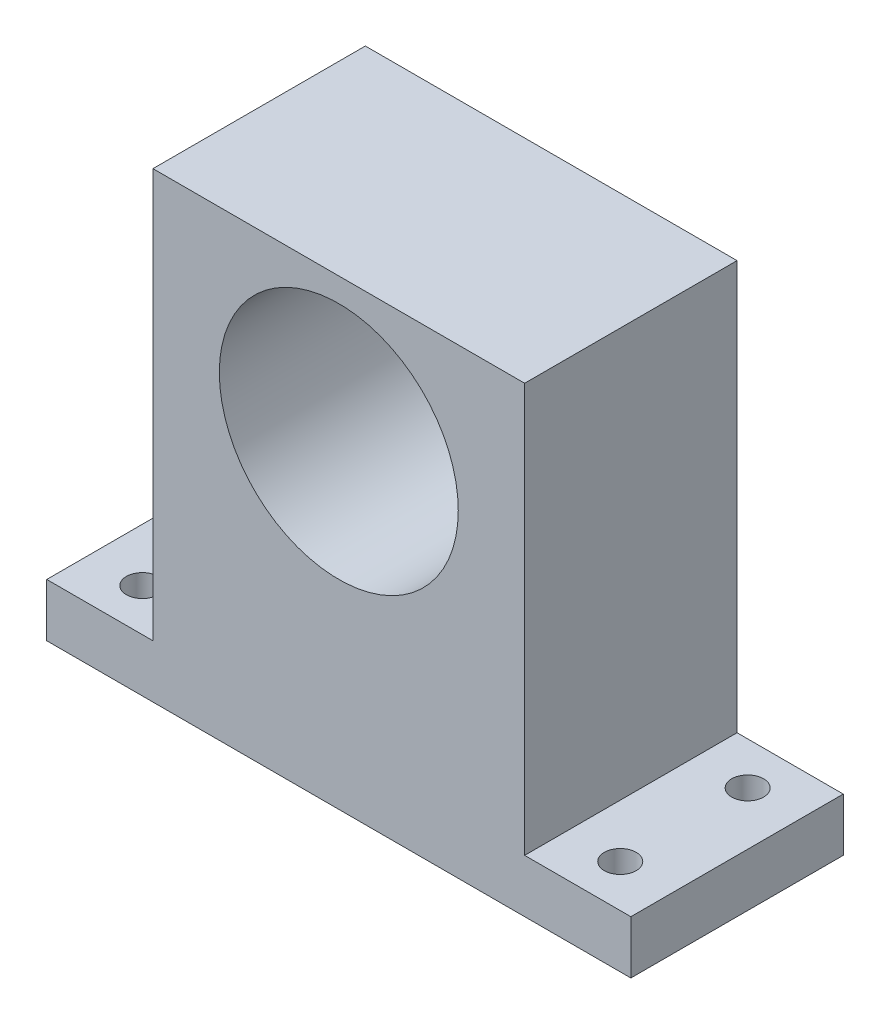
SolidWorks part; units mm, degrees
ref_plane "Спереди" through (0, 0, 0) normal (0, 0, 1) x (1, 0, 0)
ref_plane "Сверху" through (0, 0, 0) normal (0, 1, 0) x (1, 0, 0)
ref_plane "Справа" through (0, 0, 0) normal (1, 0, 0) x (0, 0, -1)
sketch "Эскиз1" plane through (0, 0, 0) normal (0, 0, 1) x (1, 0, 0)
  line L1 (-17.5, -21.75) -> (17.5, -21.75)
  line L2 (-17.5, -21.75) -> (-17.5, 21.75)
  line L3 (-17.5, 21.75) -> (17.5, 21.75)
  line L4 (17.5, -21.75) -> (17.5, 21.75)
  line L5 (-17.5, -21.75) -> (17.5, 21.75) construction
  line L6 (-17.5, 21.75) -> (17.5, -21.75) construction
  point P0 (0, 0)
  dimension "D1" = 35
  dimension "D2" = 43.5
extrude "Бобышка-Вытянуть1" add sketch "Эскиз1" along normal blind 20
sketch "Эскиз2" plane through (17.5, 0, 0) normal (1, 0, 0) x (0, 0, -1)
  line L0 (0, -21.75) -> (0, 21.75) construction
  line L1 (-20, -21.75) -> (0, -21.75)
  line L2 (-20, -21.75) -> (-20, -16.75)
  line L3 (-20, -16.75) -> (0, -16.75)
  line L4 (0, -21.75) -> (0, -16.75)
  dimension "D1" = 5
extrude "Бобышка-Вытянуть2" add sketch "Эскиз2" along normal blind 10
sketch "Эскиз3" plane through (-17.5, 0, 0) normal (-1, 0, 0) x (0, 0, 1)
  line L0 (20, 21.75) -> (20, -21.75) construction
  line L1 (0, -21.75) -> (20, -21.75)
  line L2 (0, -21.75) -> (0, -16.75)
  line L3 (0, -16.75) -> (20, -16.75)
  line L4 (20, -21.75) -> (20, -16.75)
  dimension "D1" = 5
extrude "Бобышка-Вытянуть3" add sketch "Эскиз3" along normal blind 10
sketch "Эскиз4" plane through (0, -16.75, 0) normal (0, 1, 0) x (1, 0, 0)
  line L0 (27.5, 0) -> (27.5, -20) construction
  line L1 (27.5, -20) -> (17.5, -20) construction
  line L2 (27.5, 0) -> (17.5, 0) construction
  line L3 (-27.5, -20) -> (-17.5, -20) construction
  line L4 (-27.5, -20) -> (-27.5, 0) construction
  line L5 (-27.5, 0) -> (-17.5, 0) construction
  circle A0 centre (-22.5, -16) radius 1.5
  circle A1 centre (-22.5, -4) radius 1.5
  circle A2 centre (22.5, -16) radius 1.5
  circle A3 centre (22.5, -4) radius 1.5
  point P8 (0, 0)
  point P15 (28.3893, -10.2762)
  point P20 (0, 0)
  dimension "D1" = 3
  dimension "D2" = 3
  dimension "D3" = 3
  dimension "D4" = 3
  dimension "D5" = 5
  dimension "D6" = 4
  dimension "D7" = 5
  dimension "D8" = 4
  dimension "D9" = 4
  dimension "D10" = 5
  dimension "D11" = 5
  dimension "D12" = 4
extrude "Вырез-Вытянуть2" cut sketch "Эскиз4" against normal blind 5
sketch "Эскиз5" plane through (0, 0, 0) normal (0, 0, -1) x (-1, 0, 0)
  line L0 (-17.5, -16.75) -> (-17.5, 21.75) construction
  line L1 (27.5, -21.75) -> (-27.5, -21.75) construction
  circle A0 centre (0, 8.25) radius 11.25
  dimension "D3" = 22.5
  dimension "D1" = 17.5
  dimension "D2" = 30
extrude "Вырез-Вытянуть4" cut sketch "Эскиз5" against normal blind 20
